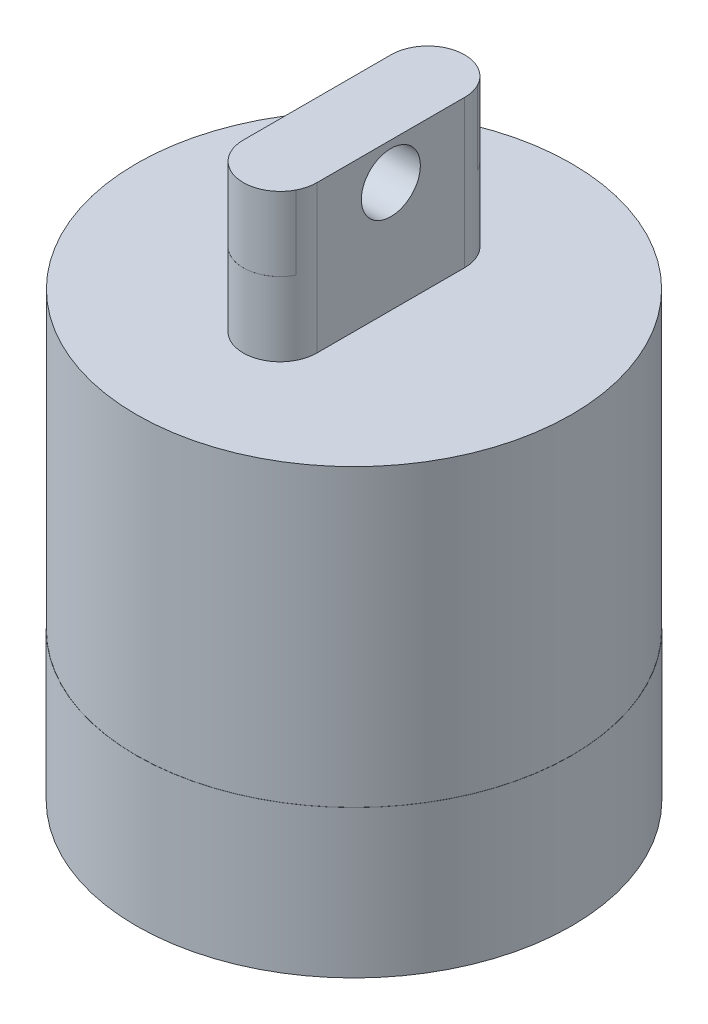
SolidWorks part; units mm, degrees
ref_plane "Front Plane" through (0, 0, 0) normal (0, 0, 1) x (1, 0, 0)
ref_plane "Top Plane" through (0, 0, 0) normal (0, 1, 0) x (1, 0, 0)
ref_plane "Right Plane" through (0, 0, 0) normal (1, 0, 0) x (0, 0, -1)
sketch "Sketch1" plane through (0, 0, 0) normal (0, 1, 0) x (1, 0, 0)
  circle A0 centre (0, 0) radius 38.1
  dimension "D1" = 76.2
extrude "Boss-Extrude1" add sketch "Sketch1" along normal blind 63.5
sketch "Sketch2" plane through (0, 0, 0) normal (0, 1, 0) x (1, 0, 0)
  line L0 (0, 38.1) -> (0, -38.1) construction
  line L1 (0, -12.7) -> (0, 12.7) construction
  line L2 (-6.35, -12.7) -> (-6.35, 12.7)
  line L3 (6.35, -12.7) -> (6.35, 12.7)
  circle A0 centre (0, 0) radius 38.1 construction
  arc A1 (-6.35, -12.7) -> (6.35, -12.7) centre (0, -12.7) ccw
  arc A2 (6.35, 12.7) -> (-6.35, 12.7) centre (0, 12.7) ccw
  point P7 (0, 0)
  dimension "D2" = 6.35
  dimension "D3" = 6.35
  dimension "D1" = 12.7
  dimension "D4" = 25.4
extrude "Boss-Extrude2" add sketch "Sketch2" along normal blind 76.2
sketch "Sketch3" plane through (0, 0, 0) normal (1, 0, 0) x (0, 0, -1)
  line L0 (0, 76.2) -> (0, 63.5) construction
  line L1 (-12.7, 76.2) -> (12.7, 76.2) construction
  line L2 (12.7, 63.5) -> (-12.7, 63.5) construction
  circle A0 centre (0, 69.85) radius 5.08
  dimension "D1" = 10.16
extrude "Cut-Extrude1" cut sketch "Sketch3" against normal blind 76.2 and the other way blind 76.2
sketch "Sketch4" plane through (0, 0, 0) normal (0, 1, 0) x (1, 0, 0)
  circle A0 centre (0, 0) radius 37.4396
  circle A1 centre (0, 0) radius 50.8
  dimension "D1" = 74.8793
  dimension "D2" = 101.6
extrude "Cut-Extrude4" cut sketch "Sketch4" against normal blind 76.2 and the other way blind 76.2
sketch "Sketch5" plane through (0, 76.2, 0) normal (0, 1, 0) x (1, 0, 0)
  line L0 (-6.35, 0) -> (6.35, 0) construction
  line L1 (-6.35, 12.7) -> (-6.35, -12.7) construction
  line L2 (6.35, -12.7) -> (6.35, 12.7) construction
  line L3 (0, -12.7182) -> (0, 12.7182) construction
  line L4 (-6.3417, -12.7182) -> (-6.3417, 12.7182)
  line L5 (6.3417, -12.7182) -> (6.3417, 12.7182)
  arc A0 (-6.3417, -12.7182) -> (6.3417, -12.7182) centre (0, -12.7182) ccw
  arc A1 (6.3417, 12.7182) -> (-6.3417, 12.7182) centre (0, 12.7182) ccw
  circle A2 centre (0, 0) radius 38.1
  point P8 (0, 0)
  dimension "D2" = 76.2
  dimension "D1" = 12.7
extrude "Cut-Extrude8" cut sketch "Sketch5" against normal blind 25.4
sketch "Sketch6" plane through (0, 0, 0) normal (0, -1, 0) x (-1, 0, 0)
  circle A0 centre (0, 0) radius 37.465
  dimension "D1" = 74.93
extrude "Boss-Extrude4" add sketch "Sketch6" along normal blind 25.4
